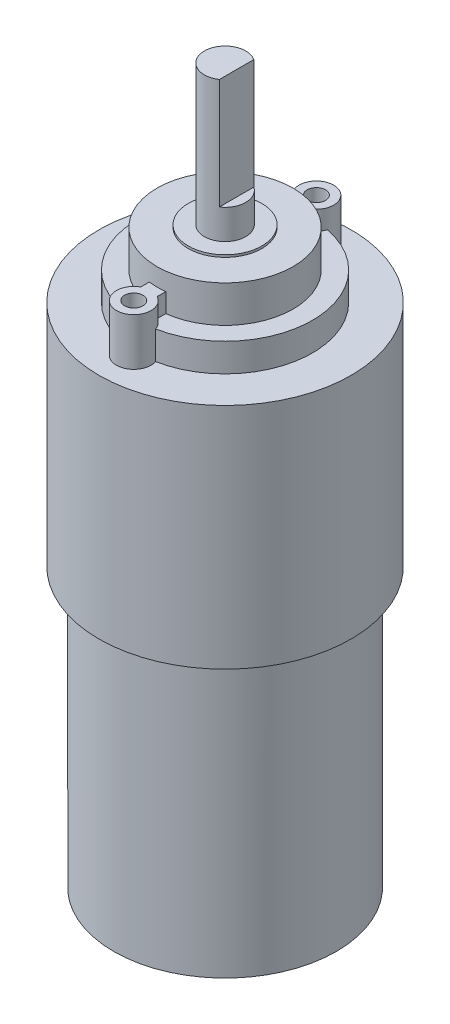
SolidWorks part; units mm, degrees
ref_plane "Front Plane" through (0, 0, 0) normal (0, 0, 1) x (1, 0, 0)
ref_plane "Top Plane" through (0, 0, 0) normal (0, 1, 0) x (1, 0, 0)
ref_plane "Right Plane" through (0, 0, 0) normal (1, 0, 0) x (0, 0, -1)
sketch "Front cylinder sketch" plane through (0, 0, 0) normal (0, 1, 0) x (1, 0, 0)
  circle A0 centre (10.0709, -22.416) radius 13.7
  dimension "D1" = 27.4
extrude "Front Cylinder" add sketch "Front cylinder sketch" along normal blind 24.8127
sketch "Mounting Point Sketch" plane through (0, 24.8127, 0) normal (0, 1, 0) x (1, 0, 0)
  line L0 (10.0709, -8.716) -> (10.0709, -36.116) construction
  line L1 (-3.6291, -22.416) -> (23.7709, -22.416) construction
  line L2 (9.1709, -14.1485) -> (9.1709, -15.0798)
  line L3 (10.9709, -14.1485) -> (10.9709, -15.0798)
  line L4 (10.9709, -30.6834) -> (10.9709, -29.7521)
  line L5 (9.1709, -30.6834) -> (9.1709, -29.7521)
  circle A0 centre (10.0709, -22.416) radius 13.7 construction
  circle A1 centre (10.0709, -12.496) radius 1
  circle A2 centre (10.0709, -32.336) radius 1
  circle A3 centre (10.0709, -12.496) radius 1.8817
  circle A4 centre (10.0709, -32.336) radius 1.8817
  circle A5 centre (10.0709, -22.416) radius 7.3911 construction
  arc A6 (9.1709, -15.0798) -> (10.9709, -15.0798) centre (10.0709, -22.416) cw
  arc A7 (9.1709, -29.7521) -> (10.9709, -29.7521) centre (10.0709, -22.416) ccw
  dimension "D1" = 2
  dimension "D2" = 19.84
  dimension "D3" = 1.8
extrude "Mounting Points" add sketch "Mounting Point Sketch" along normal blind 5.15 contours A3 A1 | L2 A6 L3 A3 | A4 A2 | A7 L5 A4 L4
sketch "Gear Mount Bottom Sketch" plane through (0, 24.8127, 0) normal (0, 1, 0) x (1, 0, 0)
  circle A0 centre (10.0709, -22.416) radius 9.5
  dimension "D1" = 19
extrude "Gear Mount Bottom" add sketch "Gear Mount Bottom Sketch" along normal blind 3.0747
sketch "Gear Mount Top Sketch" plane through (0, 27.8874, 0) normal (0, 1, 0) x (1, 0, 0)
  line L4 (10.9709, -14.1485) -> (10.9709, -15.0798)
  line L5 (9.1709, -15.0798) -> (9.1709, -14.1485)
  line L6 (9.1709, -30.6834) -> (9.1709, -29.7521)
  line L7 (10.9709, -29.7521) -> (10.9709, -30.6834)
  line L8 (10.9709, -14.1485) -> (10.9709, -15.0798)
  line L9 (9.1709, -15.0798) -> (9.1709, -14.1485)
  line L10 (9.1709, -30.6834) -> (9.1709, -29.7521)
  line L11 (10.9709, -29.7521) -> (10.9709, -30.6834)
  circle A0 centre (10.0709, -22.416) radius 7.3911
  arc A8 (10.9709, -14.1485) -> (11.8579, -13.0856) centre (10.0709, -12.496) ccw
  arc A9 (10.9709, -15.0798) -> (9.1709, -15.0798) centre (10.0709, -22.416) ccw
  arc A10 (8.284, -13.0856) -> (9.1709, -14.1485) centre (10.0709, -12.496) ccw
  arc A11 (8.284, -13.0856) -> (8.284, -31.7464) centre (10.0709, -22.416) ccw
  arc A12 (9.1709, -30.6834) -> (8.284, -31.7464) centre (10.0709, -32.336) ccw
  arc A13 (9.1709, -29.7521) -> (10.9709, -29.7521) centre (10.0709, -22.416) ccw
  arc A14 (11.8579, -31.7464) -> (10.9709, -30.6834) centre (10.0709, -32.336) ccw
  arc A15 (11.8579, -31.7464) -> (11.8579, -13.0856) centre (10.0709, -22.416) ccw
  arc A16 (10.9709, -14.1485) -> (11.8579, -13.0856) centre (10.0709, -12.496) ccw
  arc A17 (10.9709, -15.0798) -> (9.1709, -15.0798) centre (10.0709, -22.416) ccw
  arc A18 (8.284, -13.0856) -> (9.1709, -14.1485) centre (10.0709, -12.496) ccw
  arc A19 (8.284, -13.0856) -> (8.284, -31.7464) centre (10.0709, -22.416) ccw
  arc A20 (9.1709, -30.6834) -> (8.284, -31.7464) centre (10.0709, -32.336) ccw
  arc A21 (9.1709, -29.7521) -> (10.9709, -29.7521) centre (10.0709, -22.416) ccw
  arc A22 (11.8579, -31.7464) -> (10.9709, -30.6834) centre (10.0709, -32.336) ccw
  arc A23 (11.8579, -31.7464) -> (11.8579, -13.0856) centre (10.0709, -22.416) ccw
  arc M15 (10.9709, -15.0798) -> (9.1709, -15.0798) centre (10.0709, -22.416) ccw
  arc M21 (9.1709, -29.7521) -> (10.9709, -29.7521) centre (10.0709, -22.416) ccw
  dimension "D1" = 0
extrude "Gear Mount Top" add sketch "Gear Mount Top Sketch" along normal blind 4 contours A0 M21 M15
sketch "Mounting Holes Sketch" plane through (0, 24.8127, 0) normal (0, 1, 0) x (1, 0, 0)
  circle A0 centre (10.0709, -12.496) radius 1
  circle A1 centre (10.0709, -32.336) radius 1
extrude "Mounting Holes" cut sketch "Mounting Holes Sketch" along normal up to next
sketch "Gear Disk Sketch" plane through (0, 31.8874, 0) normal (0, 1, 0) x (1, 0, 0)
  circle A0 centre (10.0709, -22.416) radius 4
  circle A1 centre (10.0709, -22.416) radius 7.3911
  circle A2 centre (10.0709, -22.416) radius 7.3911
  dimension "D2" = 8
  dimension "D1" = 0
extrude "Gear disk" add sketch "Gear Disk Sketch" along normal blind 0.25 contours A0
sketch "Gear Sketch" plane through (0, 32.1374, 0) normal (0, 1, 0) x (1, 0, 0)
  circle A0 centre (10.0709, -22.416) radius 2.25
  circle A1 centre (10.0709, -22.416) radius 4
  circle A2 centre (10.0709, -22.416) radius 4
  dimension "D2" = 4.5
  dimension "D1" = 0
extrude "Gear" add sketch "Gear Sketch" along normal blind 15.225 contours A0
sketch "Gear Notch Sketch" plane through (0, 47.3624, 0) normal (0, 1, 0) x (1, 0, 0)
  line L0 (11.3209, -20.5451) -> (11.3209, -24.2868)
  arc A0 (11.3209, -20.5451) -> (11.3209, -24.2868) centre (10.0709, -22.416) cw
  circle A1 centre (10.0709, -22.416) radius 2.25
  circle A2 centre (10.0709, -22.416) radius 2.25
  circle M3 centre (10.0709, -22.416) radius 2.25
  dimension "D2" = 1.25
  dimension "D1" = 0
extrude "Gear Notch" cut sketch "Gear Notch Sketch" against normal blind 12 contours L0 M3
sketch "Back Cylinder Sketch" plane through (0, 0, 0) normal (0, -1, 0) x (1, 0, 0)
  circle A0 centre (10.0709, 22.416) radius 12.1
  circle A1 centre (10.0709, 22.416) radius 13.7
  circle A2 centre (10.0709, 22.416) radius 13.7
  dimension "D2" = 24.2
  dimension "D1" = 0
extrude "Boss-Extrude7" add sketch "Back Cylinder Sketch" along normal blind 30.2 contours A0
